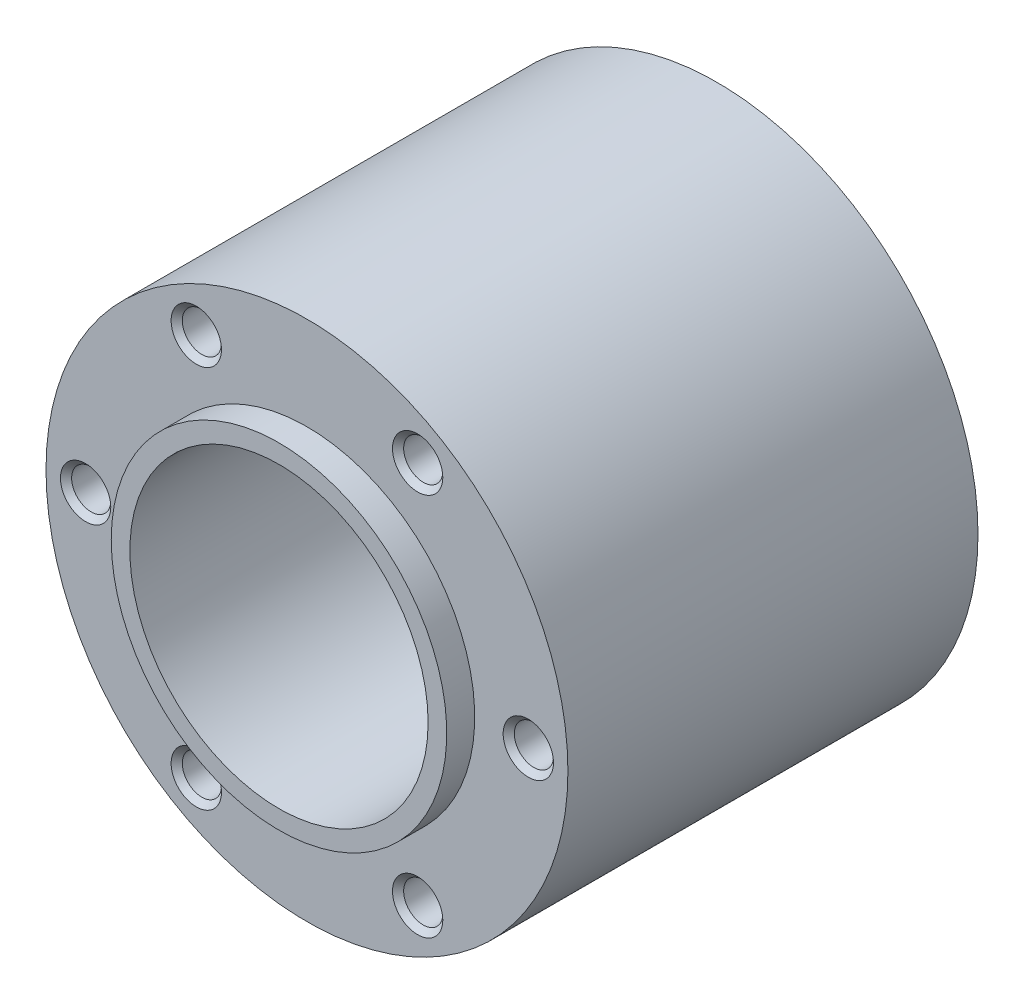
SolidWorks part; units mm, degrees
material "2024 Сплав"
ref_plane "Спереди" through (0, 0, 0) normal (0, 0, 1) x (1, 0, 0)
ref_plane "Сверху" through (0, 0, 0) normal (0, 1, 0) x (1, 0, 0)
ref_plane "Справа" through (0, 0, 0) normal (1, 0, 0) x (0, 0, -1)
sketch "Эскиз1" plane through (0, 0, 0) normal (0, 1, 0) x (1, 0, 0)
  line L0 (0, 0) -> (-18, 0)
  line L1 (-18, 0) -> (-18, 3)
  line L2 (-18, 3) -> (-28, 3)
  line L3 (-28, 3) -> (-28, 47)
  line L5 (0, 50) -> (0, 0)
  line L6 (-28, 47) -> (-18, 47)
  line L7 (-18, 47) -> (-18, 50)
  line L8 (-18, 50) -> (0, 50)
  dimension "D1" = 18
  dimension "D2" = 3
  dimension "D3" = 50
  dimension "D4" = 47
  dimension "D5" = 28
revolve "Повернуть1" add sketch "Эскиз1" angle 360 about L5
sketch "Эскиз2" plane through (0, 0, 0) normal (0, 0, 1) x (1, 0, 0)
  circle A0 centre (0, 0) radius 16
  dimension "D1" = 32
extrude "Вырез-Вытянуть1" cut sketch "Эскиз2" against normal through all both and the other way through all
hole_wizard "Сверление под метчик M51" positions "Трехмерный эскиз1" profile "Эскиз3" hole size "M5" standard "ISO" end condition up to next
sketch3d "Трехмерный эскиз1"
  line L0 (0, 0, 0) -> (23.75, 0, 0) construction
  line L1 (23.75, 0, 0) -> (23.75, 0, -3) construction
  point P0 (23.75, 0, -3)
  dimension "D1" = 3
  dimension "D2" = 23.75
cosmetic thread "Условное изображение резьбы1" parameters "D2"=5
sketch "Эскиз3" plane through (23.75, 0, -3) normal (1, 0, 0) x (0, -1, 0)
  line L0 (0, 0) -> (0, 44.001)
  line L1 (0, 44.001) -> (2.1, 44.001)
  line L2 (2.1, 44.001) -> (2.1, 0)
  line L5 (2.1, 0) -> (0, 0)
  line L11 (0, -6.35) -> (0, 107.95) construction
  dimension "Диаметр сквозного отверстия" = 4.2
  dimension "Глубина сквозного отверстия" = 44.001
pattern_circular "Круговой массив1" count 6 over 360 about axis through (0, 0, 0) along (0, 0, 1) of "Сверление под метчик M51"
chamfer "Фаска1" distance 0.6 angle 45 12 edges at (13.975, -20.5681, -3) (-9.775, -20.5681, -3) (-21.65, 0, -3) (-9.775, 20.5681, -3) (13.975, 20.5681, -3) (25.85, 0, -3) (21.65, 0, -47) (9.775, -20.5681, -47) (-13.975, -20.5681, -47) (-25.85, 0, -47) (-13.975, 20.5681, -47) (9.775, 20.5681, -47)
